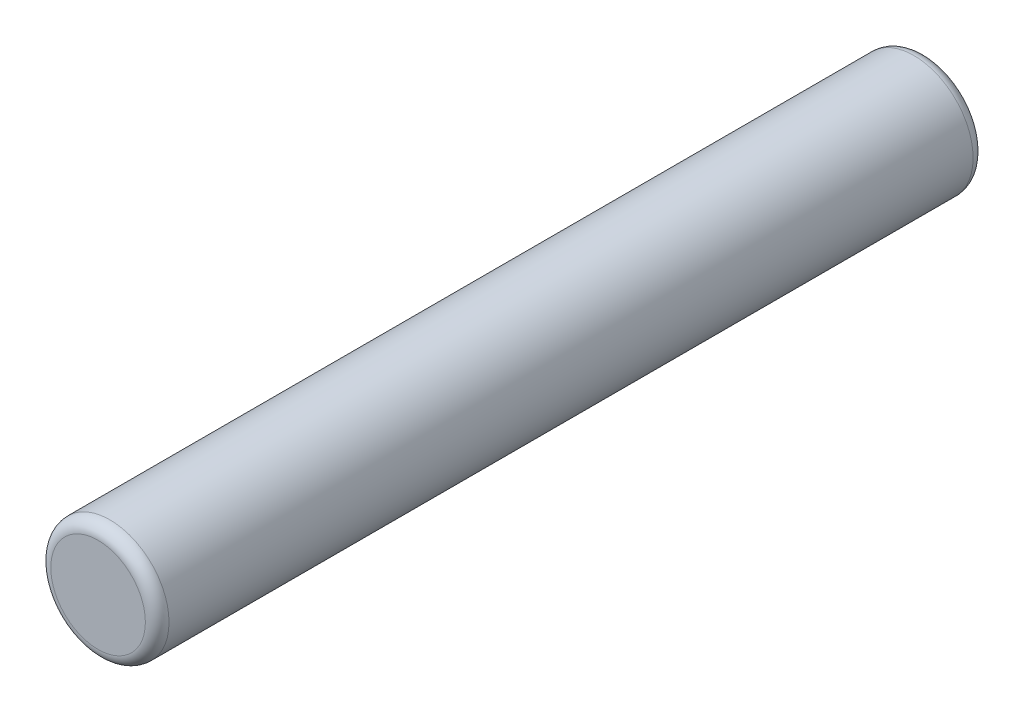
SolidWorks part; units mm, degrees
ref_plane "Front Plane" through (0, 0, 0) normal (0, 0, 1) x (1, 0, 0)
ref_plane "Top Plane" through (0, 0, 0) normal (0, 1, 0) x (1, 0, 0)
ref_plane "Right Plane" through (0, 0, 0) normal (1, 0, 0) x (0, 0, -1)
sketch "Sketch1" plane through (0, 0, 0) normal (0, 0, 1) x (1, 0, 0)
  circle A0 centre (0, 0) radius 5
  dimension "D1" = 10
extrude "Boss-Extrude1" add sketch "Sketch1" along normal mid plane 70
fillet "Fillet1" radius 1 2 edges at (5, 0, -35) (5, 0, 35)
